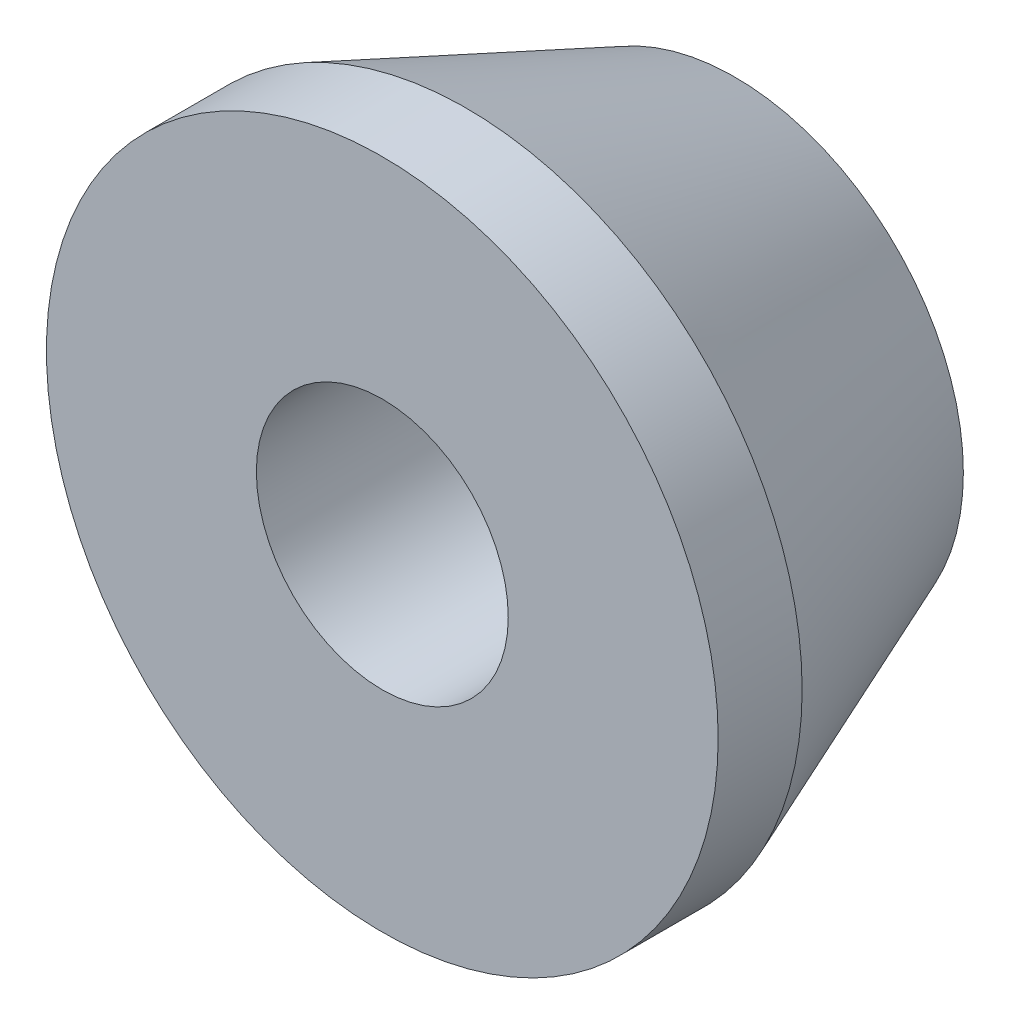
SolidWorks part; units mm, degrees
ref_plane "Front Plane" through (0, 0, 0) normal (0, 0, 1) x (1, 0, 0)
ref_plane "Top Plane" through (0, 0, 0) normal (0, 1, 0) x (1, 0, 0)
ref_plane "Right Plane" through (0, 0, 0) normal (1, 0, 0) x (0, 0, -1)
sketch "Sketch1" plane through (0, 0, 0) normal (0, 1, 0) x (1, 0, 0)
  line L0 (0, 0) -> (0, 9.3449)
  line L1 (4.7625, 0) -> (4.7625, 13.335)
  line L2 (4.7625, 13.335) -> (8.636, 13.335)
  line L3 (8.636, 13.335) -> (12.7, 3.175)
  line L4 (12.7, 3.175) -> (12.7, 0)
  line L5 (12.7, 0) -> (4.7625, 0)
  dimension "D1" = 4.7625
  dimension "D2" = 12.7
  dimension "D3" = 13.335
  dimension "D4" = 3.175
  dimension "D5" = 8.636
revolve "Revolve1" add sketch "Sketch1" angle 360 about L0
